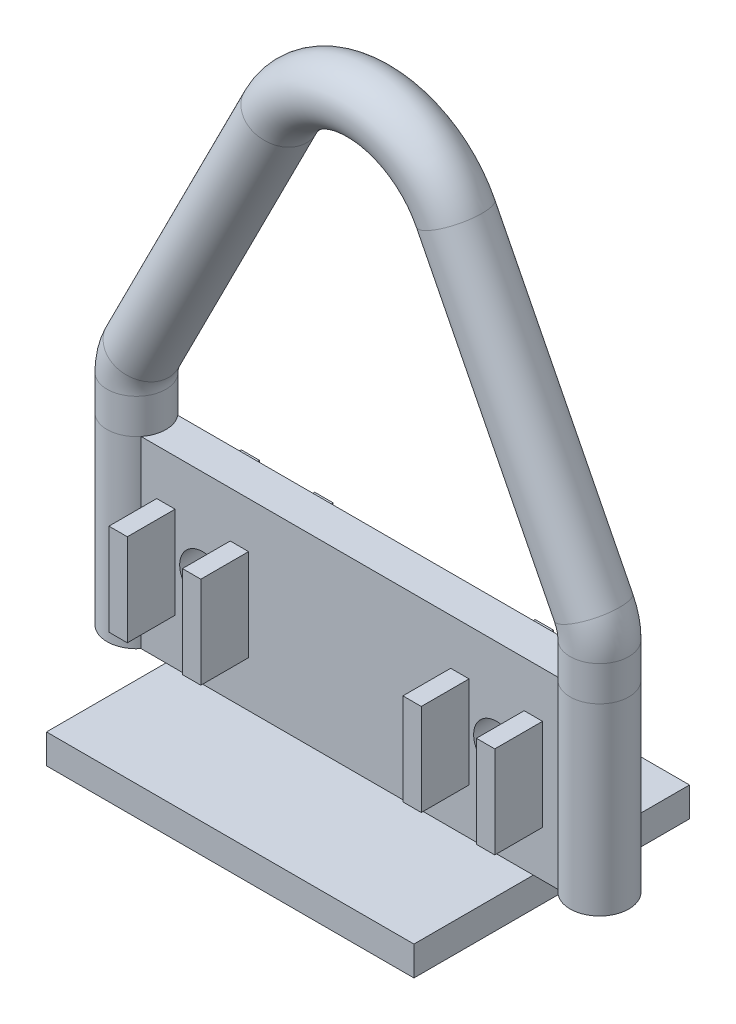
SolidWorks part; units mm, degrees
ref_plane "Front Plane" through (0, 0, 0) normal (0, 0, 1) x (1, 0, 0)
ref_plane "Top Plane" through (0, 0, 0) normal (0, 1, 0) x (1, 0, 0)
ref_plane "Right Plane" through (0, 0, 0) normal (1, 0, 0) x (0, 0, -1)
sketch "Sketch1" plane through (0, 0, 0) normal (0, 0, 1) x (1, 0, 0)
  line L0 (-108.4889, 65.8268) -> (-33.4523, 213.9467) construction
  line L1 (-126, -59.5) -> (126, -59.5) construction
  line L5 (-110, -59.5) -> (110, 59.5) construction
  line L6 (-110, 59.5) -> (110, -59.5) construction
  line L7 (0, 0) -> (0, 99.0033) construction
  line L8 (108.4889, 65.8268) -> (33.4523, 213.9467) construction
  line L9 (110, 59.5) -> (110, 40.5) construction
  line L10 (110, 40.5) -> (110, -59.5) construction
  line L11 (-110, 59.5) -> (-110, 40.5) construction
  line L12 (-110, 40.5) -> (-110, -59.5) construction
  line L13 (-126, 40.5) -> (-126, -59.5)
  line L15 (126, 40.5) -> (126, -59.5)
  line L16 (126, 59.5) -> (126, 40.5)
  line L17 (122.7619, 73.0574) -> (47.7253, 221.1773)
  line L18 (-122.7619, 73.0574) -> (-47.7253, 221.1773)
  line L19 (-126, 59.5) -> (-126, 40.5)
  line L20 (-110, -59.5) -> (110, -59.5) construction
  line L21 (-126, 40.5) -> (-126, -75.5) construction
  line L22 (-126, -75.5) -> (126, -75.5) construction
  line L23 (126, 40.5) -> (126, -75.5) construction
  arc A0 (-110, 59.5) -> (-108.4889, 65.8268) centre (-96, 59.5) cw construction
  arc A1 (-33.4523, 213.9467) -> (33.4523, 213.9467) centre (0, 197) cw construction
  arc A2 (110, 59.5) -> (108.4889, 65.8268) centre (96, 59.5) ccw construction
  arc A3 (126, 59.5) -> (122.7619, 73.0574) centre (96, 59.5) ccw
  arc A4 (-47.7253, 221.1773) -> (47.7253, 221.1773) centre (0, 197) cw
  arc A5 (-126, 59.5) -> (-122.7619, 73.0574) centre (-96, 59.5) cw
  point P0 (0, 0)
  point P13 (0, 234.5)
  dimension "D1" = 14
  dimension "D2" = 220
  dimension "D4" = 37.5
  dimension "D3" = 100
  dimension "D5" = 175
  dimension "D6" = 19
  dimension "D7" = 19
  dimension "D8" = 16
sweep "Sweep1" add path "Sketch1" circular profile diameter 32 parameters "D3"=32
sketch "Sketch8" plane through (0, 0, 0) normal (0, 0, 1) x (1, 0, 0)
  line L7 (-110, -59.5) -> (110, -59.5)
  line L8 (-110, -59.5) -> (-110, 40.5)
  line L9 (-110, 40.5) -> (110, 40.5)
  line L10 (110, -59.5) -> (110, 40.5)
extrude "Boss-Extrude1" add sketch "Sketch8" along normal mid plane 20 separate body
sketch "Sketch12" plane through (-110, 0, 0) normal (-1, 0, 0) x (0, 0, 1)
  line L4 (-10, 40.5) -> (-10, -59.5)
  line L5 (-10, -59.5) -> (10, -59.5)
  line L6 (10, -59.5) -> (10, 40.5)
  line L7 (10, 40.5) -> (-10, 40.5)
  line L8 (-10, 40.5) -> (-10, -59.5)
  line L9 (-10, -59.5) -> (10, -59.5)
  line L10 (10, -59.5) -> (10, 40.5)
  line L11 (10, 40.5) -> (-10, 40.5)
  dimension "D1" = 0
extrude "Boss-Extrude3" add sketch "Sketch12" along normal up to surface and the other way up to surface
sketch "Sketch10" plane through (0, 0, 0) normal (0, 0, 1) x (1, 0, 0)
  line L8 (-110, -59.5) -> (110, -59.5)
  line L9 (110, -59.5) -> (110, 40.5)
  line L10 (110, 40.5) -> (-110, 40.5)
  line L11 (-110, 40.5) -> (-110, -59.5)
  line L12 (-110, -59.5) -> (110, -59.5) construction
  line L13 (110, -59.5) -> (110, 40.5) construction
  line L14 (110, 40.5) -> (-110, 40.5) construction
  line L15 (-110, 40.5) -> (-110, -59.5) construction
  circle A0 centre (80, -9.5) radius 12.5
  circle A1 centre (-80, -9.5) radius 12.5
  dimension "D1" = 25
  dimension "D2" = 160
  dimension "D3" = 50
  dimension "D4" = 50
  dimension "D5" = 80
  dimension "D6" = 0
extrude "Cut-Extrude1" cut sketch "Sketch10" against normal through all both and the other way through all
sketch "Sketch11" plane through (0, 0, 0) normal (0, 0, 1) x (1, 0, 0)
  line L1 (-105, 15.5) -> (-95, 15.5)
  line L2 (-105, 15.5) -> (-105, -34.5)
  line L3 (-105, -34.5) -> (-95, -34.5)
  line L4 (-95, 15.5) -> (-95, -34.5)
  line L5 (-65, 15.5) -> (-55, 15.5)
  line L6 (-65, 15.5) -> (-65, -34.5)
  line L7 (-65, -34.5) -> (-55, -34.5)
  line L8 (-55, 15.5) -> (-55, -34.5)
  line L9 (65, 15.5) -> (55, 15.5)
  line L10 (65, 15.5) -> (65, -34.5)
  line L11 (65, -34.5) -> (55, -34.5)
  line L12 (55, 15.5) -> (55, -34.5)
  line L13 (95, 15.5) -> (105, 15.5)
  line L14 (95, 15.5) -> (95, -34.5)
  line L15 (95, -34.5) -> (105, -34.5)
  line L16 (105, 15.5) -> (105, -34.5)
  circle A4 centre (-80, -9.5) radius 12.5 construction
  circle A5 centre (-80, -9.5) radius 12.5 construction
  circle A6 centre (80, -9.5) radius 12.5 construction
  circle A7 centre (80, -9.5) radius 12.5 construction
  point P16 (0, 0)
  point P17 (0, 0)
  point P21 (0, 0)
  point P25 (0, 0)
  point P28 (-113.6502, -14.5707)
  dimension "D1" = 10
  dimension "D2" = 50
  dimension "D3" = 30
  dimension "D4" = 30
  dimension "D5" = 15
  dimension "D6" = 25
  dimension "D7" = 15
extrude "Boss-Extrude2" add sketch "Sketch11" along normal mid plane 72
sketch "Sketch15" plane through (0, 0, 0) normal (1, 0, 0) x (0, 0, -1)
  line L0 (-16, -59.5) -> (16, -59.5) construction
  line L1 (75, -59.5) -> (-75, -59.5)
  line L2 (75, -59.5) -> (75, -75.5)
  line L3 (75, -75.5) -> (-75, -75.5)
  line L4 (-75, -59.5) -> (-75, -75.5)
  point P6 (0, -59.5)
  dimension "D1" = 150
  dimension "D2" = 16
extrude "Boss-Extrude4" add sketch "Sketch15" along normal mid plane 200
